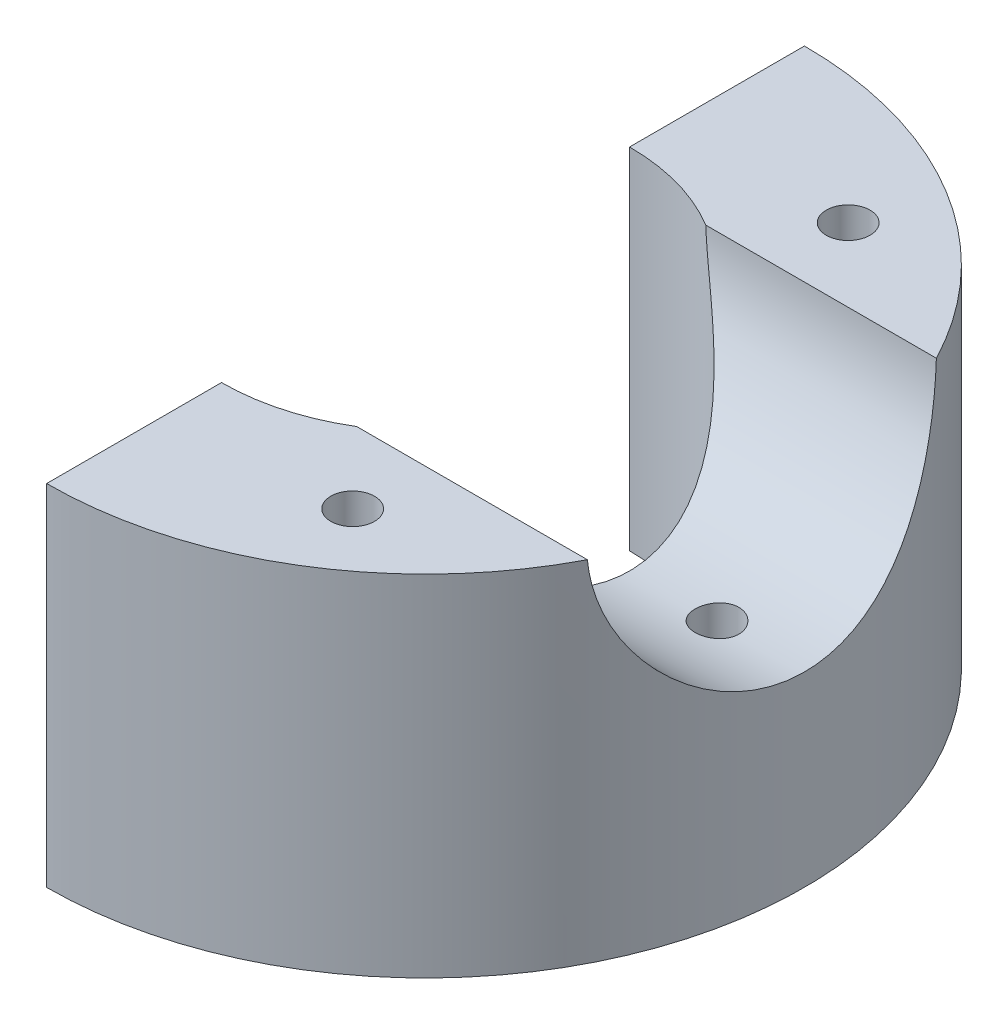
SolidWorks part; units mm, degrees
material "6061-T6 (SS)"
ref_plane "Front Plane" through (0, 0, 0) normal (0, 0, 1) x (1, 0, 0)
ref_plane "Top Plane" through (0, 0, 0) normal (0, 1, 0) x (1, 0, 0)
ref_plane "Right Plane" through (0, 0, 0) normal (1, 0, 0) x (0, 0, -1)
sketch "Sketch1" plane through (0, 0, 0) normal (0, 1, 0) x (1, 0, 0)
  line L0 (0, 82.55) -> (0, 44.45)
  line L1 (0, -44.45) -> (0, -82.55)
  arc A0 (0, -82.55) -> (0, 82.55) centre (0, 0) ccw
  arc A1 (0, -44.45) -> (0, 44.45) centre (0, 0) ccw
  dimension "D1" = 165.1
  dimension "D2" = 88.9
extrude "Boss-Extrude1" add sketch "Sketch1" along normal blind 76.2
sketch "Sketch2" plane through (0, 0, 0) normal (-1, 0, 0) x (0, 0, 1)
  line L0 (-82.55, 76.2) -> (-44.45, 76.2) construction
  line L1 (-82.55, 0) -> (-44.45, 0) construction
  line L3 (44.45, 76.2) -> (82.55, 76.2) construction
  circle A0 centre (-63.5, 57.15) radius 6.35
  circle A1 centre (-63.5, 19.05) radius 6.35
  circle A2 centre (63.5, 19.05) radius 6.35
  circle A3 centre (63.5, 57.15) radius 6.35
  point P8 (0, 0)
  point P9 (0, 0)
  point P10 (0, 0)
  point P11 (0, 0)
  point P12 (-67.8638, 58.1531)
  point P13 (67.0195, 20.8966)
  point P18 (-63.5, 76.2)
  point P21 (63.5, 76.2)
  dimension "D3" = 12.7
  dimension "D4" = 12.7
  dimension "D5" = 12.7
  dimension "D6" = 12.7
  dimension "D1" = 19.05
  dimension "D2" = 19.05
extrude "Cut-Extrude1" cut sketch "Sketch2" against normal blind 28.575
sketch "Sketch4" plane through (0, 0, 0) normal (-1, 0, 0) x (0, 0, 1)
  line L0 (44.45, 76.2) -> (-44.45, 76.2) construction
  circle A0 centre (0, 78.74) radius 38.1
  point P2 (0, 0)
  dimension "D1" = 76.2
  dimension "D2" = 2.54
extrude "Cut-Extrude3" cut sketch "Sketch4" against normal through all
sketch "Sketch5" plane through (0, 0, 0) normal (0, -1, 0) x (-1, 0, 0)
  circle A0 centre (-63.5, 0) radius 4.7625
  point P2 (0, 0)
  point P4 (-63.5, 0)
  point P5 (-62.4447, -11.5287)
  point P6 (0, 0)
  dimension "D1" = 9.525
  dimension "D2" = 63.5
extrude "Cut-Extrude4" cut sketch "Sketch5" against normal through all
sketch "Sketch6" plane through (0, 76.2, 0) normal (0, 1, 0) x (1, 0, 0)
  circle A0 centre (38.1, -53.975) radius 4.7625
  circle A1 centre (38.1, 53.975) radius 4.7625
  point P5 (0, 0)
  dimension "D3" = 9.525
  dimension "D5" = 9.525
  dimension "D1" = 53.975
  dimension "D2" = 38.1
  dimension "D4" = 53.975
extrude "Cut-Extrude5" cut sketch "Sketch6" against normal blind 28.575
